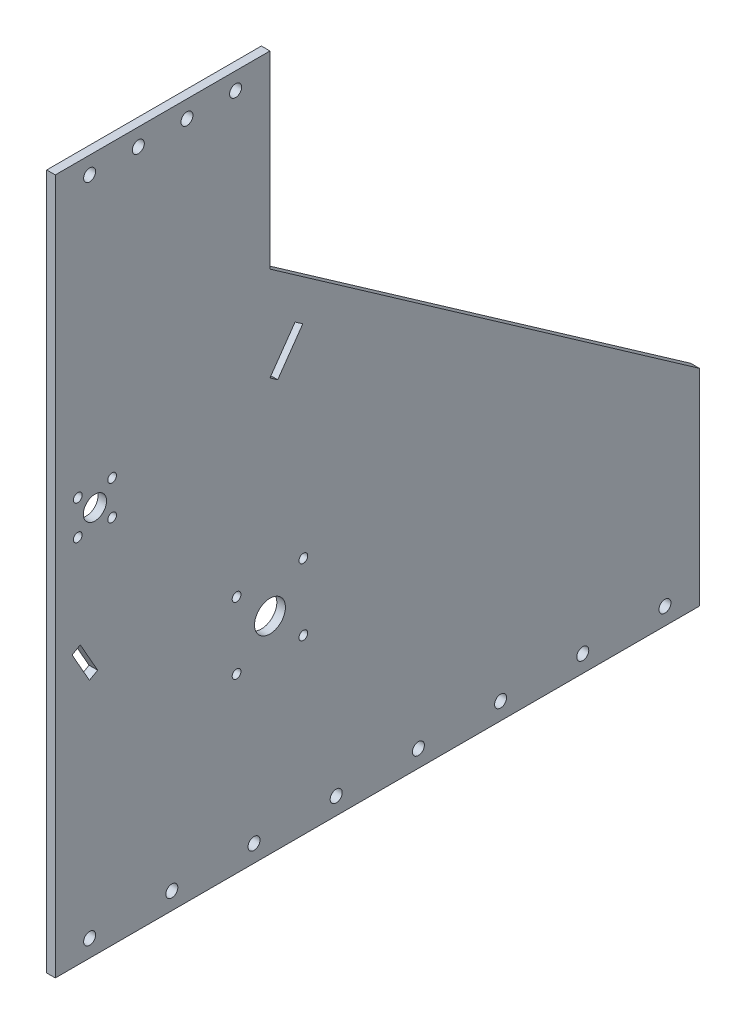
SolidWorks part; units mm, degrees
ref_plane "Ön Düzlem" through (0, 0, 0) normal (0, 0, 1) x (1, 0, 0)
ref_plane "Üst Düzlem" through (0, 0, 0) normal (0, 1, 0) x (1, 0, 0)
ref_plane "Sağ Düzlem" through (0, 0, 0) normal (1, 0, 0) x (0, 0, -1)
sketch "Çizim1" plane through (0, 0, 0) normal (1, 0, 0) x (0, 0, -1)
  line L0 (-250, 350) -> (-250, 570)
  line L1 (-250, -200) -> (500, -200) construction
  line L2 (-250, -200) -> (-250, 350)
  line L3 (-250, 350) -> (0, 350) construction
  line L4 (500, -200) -> (500, 0)
  line L5 (0, 350) -> (0, 0) construction
  line L6 (-76, 131.6359) -> (51.5805, 313.8937) construction
  line L7 (0, 350) -> (500, 0)
  line L8 (0, 350) -> (500, 350) construction
  line L9 (500, 0) -> (500, 350) construction
  line L10 (-250, 570) -> (0, 570)
  line L11 (0, 570) -> (0, 350)
  line L12 (-250, -200) -> (-250, -240)
  line L13 (-250, -240) -> (500, -240)
  line L14 (500, -240) -> (500, -200)
  line L15 (-250, 530) -> (0, 530) construction
  line L16 (-76, 131.6359) -> (-250, 131.6359) construction
  line L17 (-209.3391, 244.13) -> (-77.2372, 137.964) construction
  line L18 (-235.6946, 202.0462) -> (-82.5083, 129.5472) construction
  line L19 (51.5805, 313.8937) -> (60.592, 307.5856) construction
  line L20 (60.592, 307.5856) -> (-55.7265, 141.4162) construction
  line L21 (29.2466, 281.9881) -> (0, 240.2073)
  line L22 (29.2466, 281.9881) -> (38.2581, 275.68)
  line L23 (-131.6359, -76) -> (-250, 132.782) construction
  line L24 (-225, 224.6432) -> (-80.3694, 134.0666) construction
  line L25 (-38.8909, 38.8909) -> (38.8909, 38.8909) construction
  line L26 (-223.8121, 191.374) -> (-183.8121, 191.374) construction
  line L27 (-223.8121, 191.374) -> (-223.8121, 231.374) construction
  line L28 (-200.6816, 45.7895) -> (-220.9021, 81.4564)
  line L29 (-200.6816, 45.7895) -> (-210.2508, 40.3645)
  line L30 (-220.9021, 81.4564) -> (-230.4713, 76.0314)
  line L31 (-210.2508, 40.3645) -> (-230.4713, 76.0314)
  line L32 (-223.8121, 231.374) -> (-183.8121, 231.374) construction
  line L33 (-183.8121, 191.374) -> (-183.8121, 231.374) construction
  line L34 (-223.8121, 191.374) -> (-183.8121, 231.374) construction
  line L35 (-223.8121, 231.374) -> (-183.8121, 191.374) construction
  line L36 (-233.8121, 181.374) -> (-173.8121, 181.374) construction
  line L37 (-233.8121, 181.374) -> (-233.8121, 241.374) construction
  line L38 (-125, 530) -> (-125, 570) construction
  line L39 (0, 550) -> (-250, 550) construction
  line L40 (125, -200) -> (125, -240) construction
  line L41 (500, -220) -> (-250, -220) construction
  line L42 (0, 0) -> (-76, 131.6359) construction
  line L43 (0, 240.2073) -> (9.0116, 233.8992)
  line L44 (38.2581, 275.68) -> (9.0116, 233.8992)
  line L45 (-230.4713, 76.0314) -> (-250, 110.478) construction
  line L46 (-131.6359, -76) -> (-141.205, -81.425) construction
  line L47 (-210.2508, 40.3645) -> (-141.205, -81.425) construction
  line L48 (-233.8121, 241.374) -> (-173.8121, 241.374) construction
  line L49 (-173.8121, 181.374) -> (-173.8121, 241.374) construction
  line L50 (-233.8121, 181.374) -> (-173.8121, 241.374) construction
  line L51 (-233.8121, 241.374) -> (-173.8121, 181.374) construction
  line L52 (-38.8909, 38.8909) -> (-38.8909, -38.8909) construction
  line L53 (-38.8909, -38.8909) -> (38.8909, -38.8909) construction
  line L54 (38.8909, 38.8909) -> (38.8909, -38.8909) construction
  line L55 (-38.8909, 38.8909) -> (38.8909, -38.8909) construction
  line L56 (-38.8909, -38.8909) -> (38.8909, 38.8909) construction
  line L57 (-60, -60) -> (60, -60) construction
  line L58 (-60, -60) -> (-60, 60) construction
  line L59 (-60, 60) -> (60, 60) construction
  line L60 (60, -60) -> (60, 60) construction
  line L61 (-60, -60) -> (60, 60) construction
  line L62 (-60, 60) -> (60, -60) construction
  circle A0 centre (0, 0) radius 150 construction
  circle A1 centre (0, 0) radius 152 construction
  circle A2 centre (-225, 224.6432) radius 25 construction
  circle A3 centre (0, 0) radius 170 construction
  circle A4 centre (0, 170) radius 7 construction
  circle A5 centre (99.9235, 137.5329) radius 7 construction
  circle A6 centre (161.6796, 52.5329) radius 7 construction
  circle A7 centre (161.6796, -52.5329) radius 7 construction
  circle A8 centre (99.9235, -137.5329) radius 7 construction
  circle A9 centre (0, -170) radius 7 construction
  circle A10 centre (-99.9235, -137.5329) radius 7 construction
  circle A11 centre (-161.6796, -52.5329) radius 7 construction
  circle A12 centre (-161.6796, 52.5329) radius 7 construction
  circle A13 centre (-99.9235, 137.5329) radius 7 construction
  circle A14 centre (-80.3694, 134.0666) radius 5 construction
  circle A15 centre (-203.8121, 211.374) radius 13.5
  circle A16 centre (-183.8121, 231.374) radius 5.1
  circle A17 centre (-223.8121, 231.374) radius 5.1
  circle A18 centre (-183.8121, 191.374) radius 5.1
  circle A19 centre (-223.8121, 191.374) radius 5.1
  circle A20 centre (0, 0) radius 18
  circle A21 centre (-38.8909, 38.8909) radius 5.1
  circle A22 centre (38.8909, 38.8909) radius 5.1
  circle A23 centre (38.8909, -38.8909) radius 5.1
  circle A24 centre (-38.8909, -38.8909) radius 5.1
  circle A25 centre (0, 0) radius 55 construction
  circle A26 centre (-210, 550) radius 7
  circle A27 centre (-153.3333, 550) radius 7
  circle A28 centre (-96.6667, 550) radius 7
  circle A29 centre (-40, 550) radius 7
  circle A30 centre (0, 0) radius 190 construction
  circle A32 centre (-210, -220) radius 7
  circle A33 centre (-114.2857, -220) radius 7
  circle A34 centre (-18.5714, -220) radius 7
  circle A35 centre (77.1429, -220) radius 7
  circle A36 centre (172.8571, -220) radius 7
  circle A37 centre (268.5714, -220) radius 7
  circle A38 centre (364.2857, -220) radius 7
  circle A39 centre (460, -220) radius 7
  point P58 (0, 0)
  point P76 (37.7526, -17.0742)
  point P88 (-125, 550)
  point P105 (125, -220)
  dimension "D1" = 300
  dimension "D3" = 500
  dimension "D4" = 304
  dimension "D5" = 250
  dimension "D11" = 200
  dimension "D23" = 27
  dimension "D24" = 340
  dimension "D25" = 14
  dimension "D27" = 170.6521
  dimension "D29" = 40
  dimension "D33" = 40
  dimension "D34" = 380
  dimension "D35" = 40
  dimension "D37" = 40
  dimension "D38" = 10.2
  dimension "D19" = 10
  dimension "D20" = 50
  dimension "D30" = 14
  dimension "D39" = 60
  dimension "D43" = 36
  dimension "D44" = 110
  dimension "D45" = 10.2
  dimension "D2" = 550
  dimension "D6" = 250
  dimension "D7" = 240
  dimension "D8" = 30
  dimension "D9" = 11
  dimension "D10" = 51
  dimension "D12" = 220
  dimension "D13" = 40
  dimension "D14" = 40
  dimension "D15" = 222.474
  dimension "D16" = 140
  dimension "D17" = 90
  dimension "D18" = 11
  dimension "D21" = 41
  dimension "D22" = 240
  dimension "D28" = 46.1879
  dimension "D31" = 40
  dimension "D40" = 38.9457
  dimension "D41" = 59
  dimension "D42" = 750
  dimension "D46" = 120
  dimension "D32" = 4
  dimension "D36" = 8
  dimension "D26" = 10
extrude "Yükseklik-Ekstrüzyon1" add sketch "Çizim1" along normal blind 10
